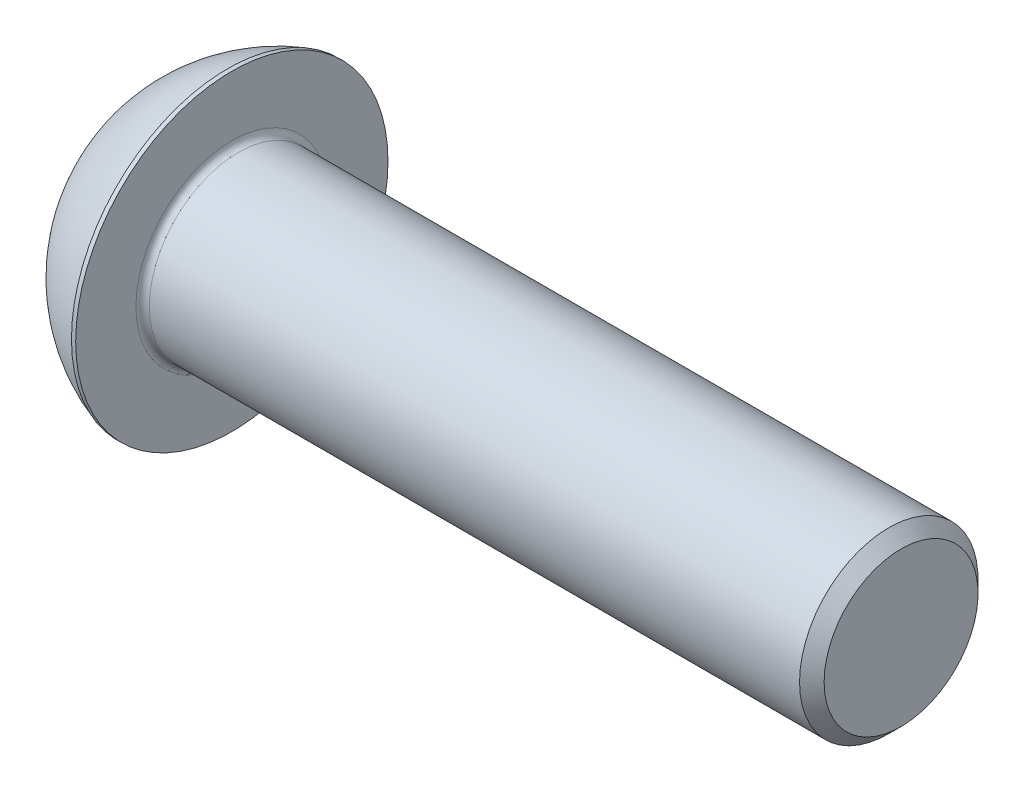
SolidWorks part; units mm, degrees
ref_plane "Plane1" through (0, 0, 0) normal (0, 0, 1) x (1, 0, 0)
ref_plane "Plane2" through (0, 0, 0) normal (0, 1, 0) x (1, 0, 0)
ref_plane "Plane3" through (0, 0, 0) normal (1, 0, 0) x (0, 0, -1)
other "Configuration Table"
sketch "BodySke" plane through (0, 0, 0) normal (0, 0, 1) x (1, 0, 0)
  line L0 (68.8, 0) -> (68.8, 6.8985)
  line L1 (67.6985, 8) -> (8.8, 8)
  line L2 (8.8, 8) -> (8.8, 14)
  line L3 (8.8, 14) -> (8.42, 14)
  line L4 (0, 0) -> (101.6, 0) construction
  line L5 (8.8, -14) -> (8.42, -14) construction
  line L6 (55.6768, -8) -> (8.8, -8) construction
  line L7 (68.8, 0) -> (0, 0)
  line L8 (0, 7) -> (0, -7) construction
  line L9 (0, 0) -> (0, 7)
  line L10 (68.8, 6.8985) -> (67.6985, 8)
  line L11 (68.8, -6.8985) -> (67.6985, -8) construction
  line L12 (10.8, 9.525) -> (10.8, -8) construction
  line L13 (8.8, 9.525) -> (8.8, -8) construction
  arc A1 (0, 7) -> (8.42, 14) centre (12.9392, 0) cw
  dimension "Head_side_ht" = 0.38
  dimension "Body_ch_ang" = 45
revolve "BaseBody" add sketch "BodySke" angle 360 about L4
cosmetic thread "ThreadCosmetic" [suppressed] parameters "Thread_length"=56, "Thread_minor"=13.797
fillet "Fillet1" radius 0.6 1 edges at (8.8, 0, 8)
sketch "Sketch2" plane through (0, 0, 0) normal (0, 0, 1) x (1, 0, 0)
  line L0 (0, 5) -> (3.0988, 5)
  line L1 (3.0988, 5) -> (5.9856, 0)
  line L3 (5.9856, 0) -> (0, 0)
  line L4 (0, 0) -> (0, 5)
  line L5 (0, -5) -> (3.0988, -5) construction
  line L6 (0, 0) -> (47.625, 0) construction
  dimension "D2" = 60
  dimension "PreBroach_depth" = 3.0988
  dimension "PreBroach_dia" = 10
revolve "PreBroach" cut sketch "Sketch2" angle 360 about L6
sketch "Sketch3" plane through (0, 0, 0) normal (1, 0, 0) x (0, 0, -1)
  line L0 (-5, -2.8868) -> (-5, 2.8868)
  line L1 (-5, 2.8868) -> (0, 5.7735)
  line L2 (0, 5.7735) -> (5, 2.8868)
  line L3 (5, 2.8868) -> (5, -2.8868)
  line L4 (5, -2.8868) -> (0, -5.7735)
  line L5 (0, -5.7735) -> (-5, -2.8868)
  dimension "D1" = 5
  dimension "D2" = 5
extrude "Hex" cut sketch "Sketch3" along normal blind 3.0988
sketch "ThdSchSke" plane through (0, 0, 0) normal (0, 0, 1) x (1, 0, 0)
  line L0 (12.8, -6.8985) -> (12.0287, -8)
  line L1 (12.8, -6.8985) -> (13.5713, -8)
  line L2 (13.5713, -8) -> (13.5713, -10)
  line L3 (-3.175, 0) -> (5.1513, 0) construction
  line L5 (13.5713, -10) -> (12.0287, -10)
  line L6 (12.0287, -10) -> (12.0287, -8)
  dimension "SideAngle" = 55
  dimension "VeeAngle" = 70
revolve "ThreadSchematic" [suppressed] cut sketch "ThdSchSke" angle 360 about L3
pattern_linear "ThdSchPat" [suppressed]
equation "\"D1@BodySke\" = \"Head_dia@BodySke\" * .5"
equation "\"Thread_minor@ThreadCosmetic\" = \"Minor_dia@BodySke\""
equation "\"D1@Sketch3\" = \"Hex_size@Sketch3\" / 2"
equation "\"D2@Sketch3\" = \"D1@Sketch3\""
equation "\"D3@Sketch3\" = \"Hex_size@Sketch3\""
equation "\"Thread_length@ThreadCosmetic\" = ((sgn( (\"Length@BodySke\" - \"Advance@BodySke\" * 2.0) - \"Thread_nom@BodySke\" )-1)*( (\"Length@BodySke\" - \"Advance@BodySke\" * 2.0) - \"Thread_nom@BodySke\" ))/-2+ \"Thread_nom@BodySke\""
equation "\"Thread_minor@ThdSchSke\" = \"Minor_dia@BodySke\""
equation "\"Diameter@ThdSchSke\" = \"Diameter@BodySke\""
equation "\"Overcut@ThdSchSke\" = \"Diameter@BodySke\" * 1.25"
equation "\"Start@ThdSchSke\" = \"Head_ht@BodySke\" + \"Length@BodySke\" - \"Thread_length@ThreadCosmetic\"  '---Non-countersunk---"
equation "\"Num_threads@ThdSchPat\" = int( \"Thread_length@ThreadCosmetic\" / \"Advance@BodySke\" + 0.999 )  + 1"
equation "\"Advance@ThdSchPat\" = \"Thread_length@ThreadCosmetic\" /  (\"Num_threads@ThdSchPat\" - 1) 'relax it"
equation "\"Num_threads@ThdSchPat\" = \"Num_threads@ThdSchPat\" - sgn( \"Num_threads@ThdSchPat\" - 1) '---chamfered tips only---"
